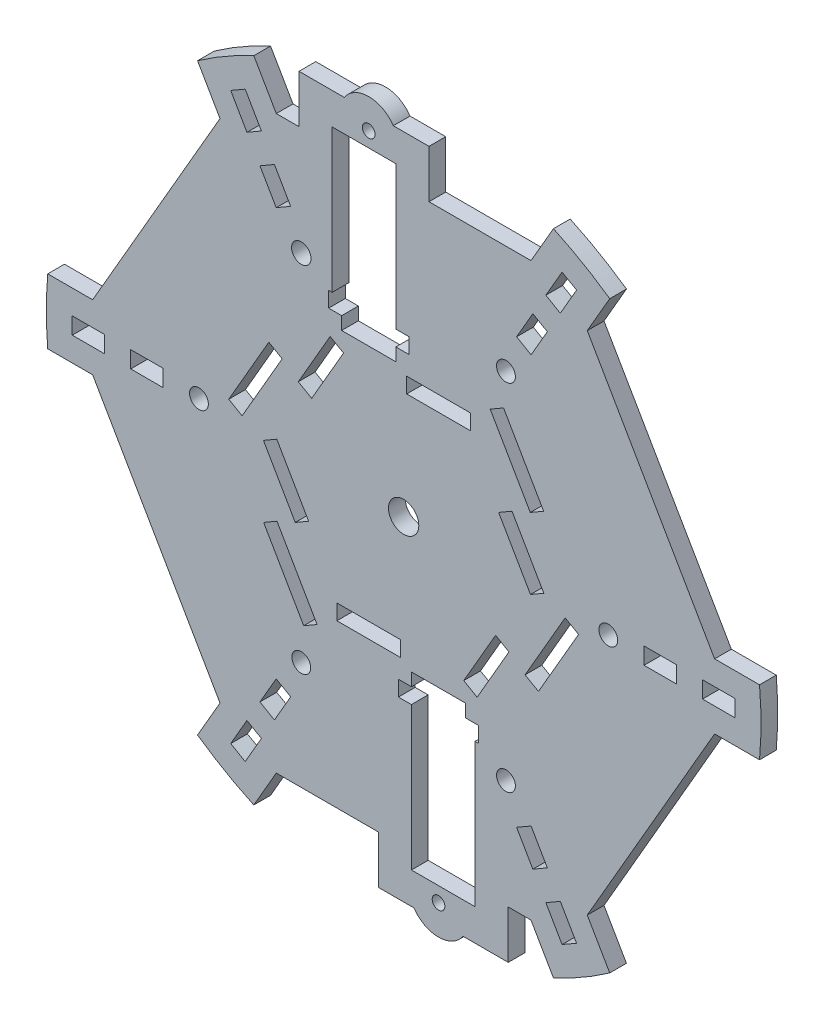
SolidWorks part; units mm, degrees
ref_plane "Front Plane" through (0, 0, 0) normal (0, 0, 1) x (1, 0, 0)
ref_plane "Top Plane" through (0, 0, 0) normal (0, 1, 0) x (1, 0, 0)
ref_plane "Right Plane" through (0, 0, 0) normal (1, 0, 0) x (0, 0, -1)
sketch "Model" plane through (0, 0, 0) normal (0, 0, 1) x (1, 0, 0)
  line L0 (33.3939, 18.31) -> (29.1071, 15.835) construction
  line L1 (43.2939, 1.1627) -> (33.3939, 18.31) construction
  line L2 (39.0071, -1.3123) -> (43.2939, 1.1627) construction
  line L3 (29.1071, 15.835) -> (39.0071, -1.3123) construction
  line L4 (32.5539, -19.765) -> (28.2671, -17.29) construction
  line L5 (22.6539, -36.9123) -> (32.5539, -19.765) construction
  line L6 (18.3671, -34.4373) -> (22.6539, -36.9123) construction
  line L7 (28.2671, -17.29) -> (18.3671, -34.4373) construction
  line L8 (-0.84, -38.075) -> (-0.84, -33.125) construction
  line L9 (-20.64, -38.075) -> (-0.84, -38.075) construction
  line L10 (-20.64, -33.125) -> (-20.64, -38.075) construction
  line L11 (-0.84, -33.125) -> (-20.64, -33.125) construction
  line L12 (-33.3939, -18.31) -> (-29.1071, -15.835) construction
  line L13 (-43.2939, -1.1627) -> (-33.3939, -18.31) construction
  line L14 (-39.0071, 1.3123) -> (-43.2939, -1.1627) construction
  line L15 (-29.1071, -15.835) -> (-39.0071, 1.3123) construction
  line L16 (-32.5539, 19.765) -> (-28.2671, 17.29) construction
  line L17 (-22.6539, 36.9123) -> (-32.5539, 19.765) construction
  line L18 (-18.3671, 34.4373) -> (-22.6539, 36.9123) construction
  line L19 (-28.2671, 17.29) -> (-18.3671, 34.4373) construction
  line L20 (38.946, 20.5225) -> (43.2328, 22.9975) construction
  line L21 (26.506, 42.0692) -> (38.946, 20.5225) construction
  line L22 (30.7928, 44.5442) -> (26.506, 42.0692) construction
  line L23 (43.2328, 22.9975) -> (30.7928, 44.5442) construction
  line L24 (37.246, -23.467) -> (41.5328, -25.942) construction
  line L25 (49.686, -1.9203) -> (37.246, -23.467) construction
  line L26 (53.9728, -4.3953) -> (49.686, -1.9203) construction
  line L27 (41.5328, -25.942) -> (53.9728, -4.3953) construction
  line L28 (2.3, -43.9895) -> (-1.7, -43.9895) construction
  line L29 (2.3, -40.0395) -> (2.3, -43.9895) construction
  line L30 (19.18, -40.0395) -> (2.3, -40.0395) construction
  line L31 (19.18, -43.9895) -> (19.18, -40.0395) construction
  line L32 (23.18, -43.9895) -> (19.18, -43.9895) construction
  line L33 (23.18, -48.9395) -> (23.18, -43.9895) construction
  line L34 (22.1, -48.9395) -> (23.18, -48.9395) construction
  line L35 (22.1, -93.0395) -> (22.1, -48.9395) construction
  line L36 (2.3, -93.0395) -> (22.1, -93.0395) construction
  line L37 (2.3, -48.9395) -> (2.3, -93.0395) construction
  line L38 (-1.7, -48.9395) -> (2.3, -48.9395) construction
  line L39 (-1.7, -43.9895) -> (-1.7, -48.9395) construction
  line L40 (-38.946, -20.5225) -> (-43.2328, -22.9975) construction
  line L41 (-26.506, -42.0692) -> (-38.946, -20.5225) construction
  line L42 (-30.7928, -44.5442) -> (-26.506, -42.0692) construction
  line L43 (-43.2328, -22.9975) -> (-30.7928, -44.5442) construction
  line L44 (-37.246, 23.467) -> (-41.5328, 25.942) construction
  line L45 (-49.686, 1.9203) -> (-37.246, 23.467) construction
  line L46 (-53.9728, 4.3953) -> (-49.686, 1.9203) construction
  line L47 (-41.5328, 25.942) -> (-53.9728, 4.3953) construction
  line L48 (0.84, 38.075) -> (0.84, 33.125) construction
  line L49 (20.64, 38.075) -> (0.84, 38.075) construction
  line L50 (20.64, 33.125) -> (20.64, 38.075) construction
  line L51 (0.84, 33.125) -> (20.64, 33.125) construction
  line L52 (-2.3, 43.9895) -> (1.7, 43.9895) construction
  line L53 (-2.3, 40.0395) -> (-2.3, 43.9895) construction
  line L54 (-19.18, 40.0395) -> (-2.3, 40.0395) construction
  line L55 (-19.18, 43.9895) -> (-19.18, 40.0395) construction
  line L56 (-23.18, 43.9895) -> (-19.18, 43.9895) construction
  line L57 (-23.18, 48.9395) -> (-23.18, 43.9895) construction
  line L58 (-22.1, 48.9395) -> (-23.18, 48.9395) construction
  line L59 (-22.1, 93.0395) -> (-22.1, 48.9395) construction
  line L60 (-2.3, 93.0395) -> (-22.1, 93.0395) construction
  line L61 (-2.3, 48.9395) -> (-2.3, 93.0395) construction
  line L62 (1.7, 48.9395) -> (-2.3, 48.9395) construction
  line L63 (1.7, 43.9895) -> (1.7, 48.9395) construction
  line L64 (34.6334, 65.3368) -> (39.2666, 62.6618) construction
  line L65 (39.7334, 74.1702) -> (34.6334, 65.3368) construction
  line L66 (44.3666, 71.4952) -> (39.7334, 74.1702) construction
  line L67 (39.2666, 62.6618) -> (44.3666, 71.4952) construction
  line L68 (73.9, 2.675) -> (73.9, -2.675) construction
  line L69 (84.1, 2.675) -> (73.9, 2.675) construction
  line L70 (84.1, -2.675) -> (84.1, 2.675) construction
  line L71 (73.9, -2.675) -> (84.1, -2.675) construction
  line L72 (39.2666, -62.6618) -> (34.6334, -65.3368) construction
  line L73 (44.3666, -71.4952) -> (39.2666, -62.6618) construction
  line L74 (39.7334, -74.1702) -> (44.3666, -71.4952) construction
  line L75 (34.6334, -65.3368) -> (39.7334, -74.1702) construction
  line L76 (-34.6334, -65.3368) -> (-39.2666, -62.6618) construction
  line L77 (-39.7334, -74.1702) -> (-34.6334, -65.3368) construction
  line L78 (-44.3666, -71.4952) -> (-39.7334, -74.1702) construction
  line L79 (-39.2666, -62.6618) -> (-44.3666, -71.4952) construction
  line L80 (-73.9, -2.675) -> (-73.9, 2.675) construction
  line L81 (-84.1, -2.675) -> (-73.9, -2.675) construction
  line L82 (-84.1, 2.675) -> (-84.1, -2.675) construction
  line L83 (-73.9, 2.675) -> (-84.1, 2.675) construction
  line L84 (-39.2666, 62.6618) -> (-34.6334, 65.3368) construction
  line L85 (-44.3666, 71.4952) -> (-39.2666, 62.6618) construction
  line L86 (-39.7334, 74.1702) -> (-44.3666, 71.4952) construction
  line L87 (-34.6334, 65.3368) -> (-39.7334, 74.1702) construction
  line L88 (-56.6362, 77.8962) -> (-95.7785, 10.0998) construction
  line L89 (-95.7785, 10.0998) -> (-109.6358, 10.0998) construction
  line L90 (-109.6357, -10.1005) -> (-95.7779, -10.1005) construction
  line L91 (-95.7779, -10.1005) -> (-56.6357, -77.8969) construction
  line L92 (-56.6357, -77.8969) -> (-63.5643, -89.8976) construction
  line L93 (-46.071, -99.9974) -> (-39.1423, -87.9964) construction
  line L94 (-39.1423, -87.9964) -> (-7.9, -87.9964) construction
  line L95 (-7.9, -87.9964) -> (-7.9, -102.7645) construction
  line L96 (-7.9, -102.7645) -> (3.1242, -102.7645) construction
  line L97 (18.3558, -102.7645) -> (32.3, -102.7645) construction
  line L98 (32.3, -102.7645) -> (32.3, -87.9964) construction
  line L99 (32.3, -87.9964) -> (39.1423, -87.9964) construction
  line L100 (39.1423, -87.9964) -> (46.071, -99.9974) construction
  line L101 (63.5645, -89.8975) -> (56.6358, -77.8966) construction
  line L102 (56.6358, -77.8966) -> (95.778, -10.1002) construction
  line L103 (95.778, -10.1002) -> (109.6357, -10.1002) construction
  line L104 (109.6358, 10.0995) -> (95.7786, 10.0995) construction
  line L105 (95.7786, 10.0995) -> (56.6363, 77.8959) construction
  line L106 (56.6363, 77.8959) -> (63.5652, 89.8971) construction
  line L107 (46.071, 99.9974) -> (39.1423, 87.9964) construction
  line L108 (39.1423, 87.9964) -> (7.9, 87.9964) construction
  line L109 (7.9, 87.9964) -> (7.9, 102.7645) construction
  line L110 (7.9, 102.7645) -> (-3.1242, 102.7645) construction
  line L111 (-18.3558, 102.7645) -> (-32.3, 102.7645) construction
  line L112 (-32.3, 102.7645) -> (-32.3, 87.9964) construction
  line L113 (-32.3, 87.9964) -> (-39.1423, 87.9964) construction
  line L114 (-39.1423, 87.9964) -> (-46.071, 99.9974) construction
  line L115 (-63.565, 89.8972) -> (-56.6362, 77.8962) construction
  line L116 (-48.2666, 78.2502) -> (-43.6334, 80.9252) construction
  line L117 (-53.3666, 87.0837) -> (-48.2666, 78.2502) construction
  line L118 (-48.7334, 89.7587) -> (-53.3666, 87.0837) construction
  line L119 (-43.6334, 80.9252) -> (-48.7334, 89.7587) construction
  line L120 (-91.9, -2.675) -> (-91.9, 2.675) construction
  line L121 (-102.1, -2.675) -> (-91.9, -2.675) construction
  line L122 (-102.1, 2.675) -> (-102.1, -2.675) construction
  line L123 (-91.9, 2.675) -> (-102.1, 2.675) construction
  line L124 (-43.6334, -80.9252) -> (-48.2666, -78.2502) construction
  line L125 (-48.7334, -89.7587) -> (-43.6334, -80.9252) construction
  line L126 (-53.3666, -87.0837) -> (-48.7334, -89.7587) construction
  line L127 (-48.2666, -78.2502) -> (-53.3666, -87.0837) construction
  line L128 (48.2666, -78.2502) -> (43.6334, -80.9252) construction
  line L129 (53.3666, -87.0837) -> (48.2666, -78.2502) construction
  line L130 (48.7334, -89.7587) -> (53.3666, -87.0837) construction
  line L131 (43.6334, -80.9252) -> (48.7334, -89.7587) construction
  line L132 (91.9, 2.675) -> (91.9, -2.675) construction
  line L133 (102.1, 2.675) -> (91.9, 2.675) construction
  line L134 (102.1, -2.675) -> (102.1, 2.675) construction
  line L135 (91.9, -2.675) -> (102.1, -2.675) construction
  line L136 (43.6334, 80.9252) -> (48.2666, 78.2502) construction
  line L137 (48.7334, 89.7587) -> (43.6334, 80.9252) construction
  line L138 (53.3666, 87.0837) -> (48.7334, 89.7587) construction
  line L139 (48.2666, 78.2502) -> (53.3666, 87.0837) construction
  line L140 (-56.5207, 77.8962) -> (-95.7207, 9.9998)
  line L141 (-95.7207, 9.9998) -> (-109.5445, 9.9998)
  line L142 (-109.5445, -10.0005) -> (-95.7202, -10.0005)
  line L143 (-95.7202, -10.0005) -> (-56.5202, -77.8969)
  line L144 (-56.5202, -77.8969) -> (-63.4321, -89.8686)
  line L145 (-46.112, -99.8683) -> (-39.2, -87.8964)
  line L146 (-39.2, -87.8964) -> (-7.8, -87.8964)
  line L147 (-7.8, -87.8964) -> (-7.8, -102.6645)
  line L148 (-7.8, -102.6645) -> (3.1769, -102.6645)
  line L149 (18.3031, -102.6645) -> (32.2, -102.6645)
  line L150 (32.2, -102.6645) -> (32.2, -87.8964)
  line L151 (32.2, -87.8964) -> (39.2, -87.8964)
  line L152 (39.2, -87.8964) -> (46.112, -99.8683)
  line L153 (63.4323, -89.8685) -> (56.5203, -77.8966)
  line L154 (56.5203, -77.8966) -> (95.7203, -10.0002)
  line L155 (95.7203, -10.0002) -> (109.5445, -10.0002)
  line L156 (109.5446, 9.9995) -> (95.7208, 9.9995)
  line L157 (95.7208, 9.9995) -> (56.5208, 77.8959)
  line L158 (56.5208, 77.8959) -> (63.4329, 89.868)
  line L159 (46.112, 99.8683) -> (39.2, 87.8964)
  line L160 (39.2, 87.8964) -> (7.8, 87.8964)
  line L161 (7.8, 87.8964) -> (7.8, 102.6645)
  line L162 (7.8, 102.6645) -> (-3.1769, 102.6645)
  line L163 (-18.3031, 102.6645) -> (-32.2, 102.6645)
  line L164 (-32.2, 102.6645) -> (-32.2, 87.8964)
  line L165 (-32.2, 87.8964) -> (-39.2, 87.8964)
  line L166 (-39.2, 87.8964) -> (-46.112, 99.8683)
  line L167 (-63.4327, 89.8682) -> (-56.5207, 77.8962)
  line L168 (74, 2.575) -> (74, -2.575)
  line L169 (74, -2.575) -> (84, -2.575)
  line L170 (84, -2.575) -> (84, 2.575)
  line L171 (84, 2.575) -> (74, 2.575)
  line L172 (92, 2.575) -> (92, -2.575)
  line L173 (92, -2.575) -> (102, -2.575)
  line L174 (102, -2.575) -> (102, 2.575)
  line L175 (102, 2.575) -> (92, 2.575)
  line L176 (34.77, 65.3734) -> (39.23, 62.7984)
  line L177 (39.23, 62.7984) -> (44.23, 71.4586)
  line L178 (44.23, 71.4586) -> (39.77, 74.0336)
  line L179 (39.77, 74.0336) -> (34.77, 65.3734)
  line L180 (43.77, 80.9618) -> (48.23, 78.3868)
  line L181 (48.23, 78.3868) -> (53.23, 87.0471)
  line L182 (53.23, 87.0471) -> (48.77, 89.6221)
  line L183 (48.77, 89.6221) -> (43.77, 80.9618)
  line L184 (-48.23, 78.3868) -> (-43.77, 80.9618)
  line L185 (-43.77, 80.9618) -> (-48.77, 89.6221)
  line L186 (-48.77, 89.6221) -> (-53.23, 87.0471)
  line L187 (-53.23, 87.0471) -> (-48.23, 78.3868)
  line L188 (-39.23, 62.7984) -> (-34.77, 65.3734)
  line L189 (-34.77, 65.3734) -> (-39.77, 74.0336)
  line L190 (-39.77, 74.0336) -> (-44.23, 71.4586)
  line L191 (-44.23, 71.4586) -> (-39.23, 62.7984)
  line L192 (-74, -2.575) -> (-74, 2.575)
  line L193 (-74, 2.575) -> (-84, 2.575)
  line L194 (-84, 2.575) -> (-84, -2.575)
  line L195 (-84, -2.575) -> (-74, -2.575)
  line L196 (-92, -2.575) -> (-92, 2.575)
  line L197 (-92, 2.575) -> (-102, 2.575)
  line L198 (-102, 2.575) -> (-102, -2.575)
  line L199 (-102, -2.575) -> (-92, -2.575)
  line L200 (-34.77, -65.3734) -> (-39.23, -62.7984)
  line L201 (-39.23, -62.7984) -> (-44.23, -71.4586)
  line L202 (-44.23, -71.4586) -> (-39.77, -74.0336)
  line L203 (-39.77, -74.0336) -> (-34.77, -65.3734)
  line L204 (-43.77, -80.9618) -> (-48.23, -78.3868)
  line L205 (-48.23, -78.3868) -> (-53.23, -87.0471)
  line L206 (-53.23, -87.0471) -> (-48.77, -89.6221)
  line L207 (-48.77, -89.6221) -> (-43.77, -80.9618)
  line L208 (39.23, -62.7984) -> (34.77, -65.3734)
  line L209 (34.77, -65.3734) -> (39.77, -74.0336)
  line L210 (39.77, -74.0336) -> (44.23, -71.4586)
  line L211 (44.23, -71.4586) -> (39.23, -62.7984)
  line L212 (48.23, -78.3868) -> (43.77, -80.9618)
  line L213 (43.77, -80.9618) -> (48.77, -89.6221)
  line L214 (48.77, -89.6221) -> (53.23, -87.0471)
  line L215 (53.23, -87.0471) -> (48.23, -78.3868)
  line L216 (33.3573, 18.1734) -> (29.2437, 15.7984)
  line L217 (29.2437, 15.7984) -> (39.0437, -1.1757)
  line L218 (39.0437, -1.1757) -> (43.1573, 1.1993)
  line L219 (43.1573, 1.1993) -> (33.3573, 18.1734)
  line L220 (32.4173, -19.8016) -> (28.3037, -17.4266)
  line L221 (28.3037, -17.4266) -> (18.5037, -34.4007)
  line L222 (18.5037, -34.4007) -> (22.6173, -36.7757)
  line L223 (22.6173, -36.7757) -> (32.4173, -19.8016)
  line L224 (-0.94, -37.975) -> (-0.94, -33.225)
  line L225 (-0.94, -33.225) -> (-20.54, -33.225)
  line L226 (-20.54, -33.225) -> (-20.54, -37.975)
  line L227 (-20.54, -37.975) -> (-0.94, -37.975)
  line L228 (-33.3573, -18.1734) -> (-29.2437, -15.7984)
  line L229 (-29.2437, -15.7984) -> (-39.0437, 1.1757)
  line L230 (-39.0437, 1.1757) -> (-43.1573, -1.1993)
  line L231 (-43.1573, -1.1993) -> (-33.3573, -18.1734)
  line L232 (-32.4173, 19.8016) -> (-28.3037, 17.4266)
  line L233 (-28.3037, 17.4266) -> (-18.5037, 34.4007)
  line L234 (-18.5037, 34.4007) -> (-22.6173, 36.7757)
  line L235 (-22.6173, 36.7757) -> (-32.4173, 19.8016)
  line L236 (38.9826, 20.6591) -> (43.0962, 23.0341)
  line L237 (43.0962, 23.0341) -> (30.7562, 44.4076)
  line L238 (30.7562, 44.4076) -> (26.6426, 42.0326)
  line L239 (26.6426, 42.0326) -> (38.9826, 20.6591)
  line L240 (37.3826, -23.4304) -> (41.4962, -25.8054)
  line L241 (41.4962, -25.8054) -> (53.8362, -4.4319)
  line L242 (53.8362, -4.4319) -> (49.7226, -2.0569)
  line L243 (49.7226, -2.0569) -> (37.3826, -23.4304)
  line L244 (2.4, -44.0895) -> (-1.6, -44.0895)
  line L245 (-1.6, -44.0895) -> (-1.6, -48.8395)
  line L246 (-1.6, -48.8395) -> (2.4, -48.8395)
  line L247 (2.4, -48.8395) -> (2.4, -92.9395)
  line L248 (2.4, -92.9395) -> (22, -92.9395)
  line L249 (22, -92.9395) -> (22, -48.8395)
  line L250 (22, -48.8395) -> (23.08, -48.8395)
  line L251 (23.08, -48.8395) -> (23.08, -44.0895)
  line L252 (23.08, -44.0895) -> (19.08, -44.0895)
  line L253 (19.08, -44.0895) -> (19.08, -40.1395)
  line L254 (19.08, -40.1395) -> (2.4, -40.1395)
  line L255 (2.4, -40.1395) -> (2.4, -44.0895)
  line L256 (-38.9826, -20.6591) -> (-43.0962, -23.0341)
  line L257 (-43.0962, -23.0341) -> (-30.7562, -44.4076)
  line L258 (-30.7562, -44.4076) -> (-26.6426, -42.0326)
  line L259 (-26.6426, -42.0326) -> (-38.9826, -20.6591)
  line L260 (-37.3826, 23.4304) -> (-41.4962, 25.8054)
  line L261 (-41.4962, 25.8054) -> (-53.8362, 4.4319)
  line L262 (-53.8362, 4.4319) -> (-49.7226, 2.0569)
  line L263 (-49.7226, 2.0569) -> (-37.3826, 23.4304)
  line L264 (0.94, 37.975) -> (0.94, 33.225)
  line L265 (0.94, 33.225) -> (20.54, 33.225)
  line L266 (20.54, 33.225) -> (20.54, 37.975)
  line L267 (20.54, 37.975) -> (0.94, 37.975)
  line L268 (-2.4, 44.0895) -> (1.6, 44.0895)
  line L269 (1.6, 44.0895) -> (1.6, 48.8395)
  line L270 (1.6, 48.8395) -> (-2.4, 48.8395)
  line L271 (-2.4, 48.8395) -> (-2.4, 92.9395)
  line L272 (-2.4, 92.9395) -> (-22, 92.9395)
  line L273 (-22, 92.9395) -> (-22, 48.8395)
  line L274 (-22, 48.8395) -> (-23.08, 48.8395)
  line L275 (-23.08, 48.8395) -> (-23.08, 44.0895)
  line L276 (-23.08, 44.0895) -> (-19.08, 44.0895)
  line L277 (-19.08, 44.0895) -> (-19.08, 40.1395)
  line L278 (-19.08, 40.1395) -> (-2.4, 40.1395)
  line L279 (-2.4, 40.1395) -> (-2.4, 44.0895)
  circle A0 centre (-63, 0) radius 3 construction
  circle A1 centre (-31.5, -54.5596) radius 3 construction
  circle A2 centre (31.5, -54.5596) radius 3 construction
  circle A3 centre (63, 0) radius 3 construction
  circle A4 centre (31.5, 54.5596) radius 3 construction
  circle A5 centre (-31.5, 54.5596) radius 3.1 construction
  circle A6 centre (-10.74, 97.5145) radius 2.05 construction
  arc A7 (-109.6358, 10.0998) -> (-109.6357, -10.1005) centre (0, 0) ccw construction
  arc A8 (-63.5643, -89.8976) -> (-46.071, -99.9974) centre (0, 0) ccw construction
  arc A9 (3.1242, -102.7645) -> (18.3558, -102.7645) centre (10.74, -97.5145) ccw construction
  arc A10 (46.071, -99.9974) -> (63.5645, -89.8975) centre (0, 0) ccw construction
  arc A11 (109.6357, -10.1002) -> (109.6358, 10.0995) centre (0, 0) ccw construction
  arc A12 (63.5652, 89.8971) -> (46.071, 99.9974) centre (0, 0) ccw construction
  arc A13 (-3.1242, 102.7645) -> (-18.3558, 102.7645) centre (-10.74, 97.5145) ccw construction
  arc A14 (-46.071, 99.9974) -> (-63.565, 89.8972) centre (0, 0) ccw construction
  circle A15 centre (0, 0) radius 4.765 construction
  circle A16 centre (10.74, -97.5145) radius 2.05 construction
  arc A17 (-109.5445, 9.9998) -> (-109.5445, -10.0005) centre (0, 0) ccw
  arc A18 (-63.4321, -89.8686) -> (-46.112, -99.8683) centre (0, 0) ccw
  arc A19 (3.1769, -102.6645) -> (18.3031, -102.6645) centre (10.74, -97.5145) ccw
  arc A20 (46.112, -99.8683) -> (63.4323, -89.8685) centre (0, 0) ccw
  arc A21 (109.5445, -10.0002) -> (109.5446, 9.9995) centre (0, 0) ccw
  arc A22 (63.4329, 89.868) -> (46.112, 99.8683) centre (0, 0) ccw
  arc A23 (-3.1769, 102.6645) -> (-18.3031, 102.6645) centre (-10.74, 97.5145) ccw
  arc A24 (-46.112, 99.8683) -> (-63.4327, 89.8682) centre (0, 0) ccw
  circle A25 centre (-63, 0) radius 2.9
  circle A26 centre (-31.5, -54.5596) radius 2.9
  circle A27 centre (31.5, -54.5596) radius 2.9
  circle A28 centre (63, 0) radius 2.9
  circle A29 centre (31.5, 54.5596) radius 2.9
  circle A30 centre (-31.5, 54.5596) radius 3
  circle A31 centre (0, 0) radius 4.665
  circle A32 centre (10.74, -97.5145) radius 1.95
  circle A33 centre (-10.74, 97.5145) radius 1.95
  dimension "D1" = 0.1
  dimension "D2" = 0.1
  dimension "D3" = 0.1
extrude "Boss-Extrude1" add sketch "Model" along normal blind 5.15
